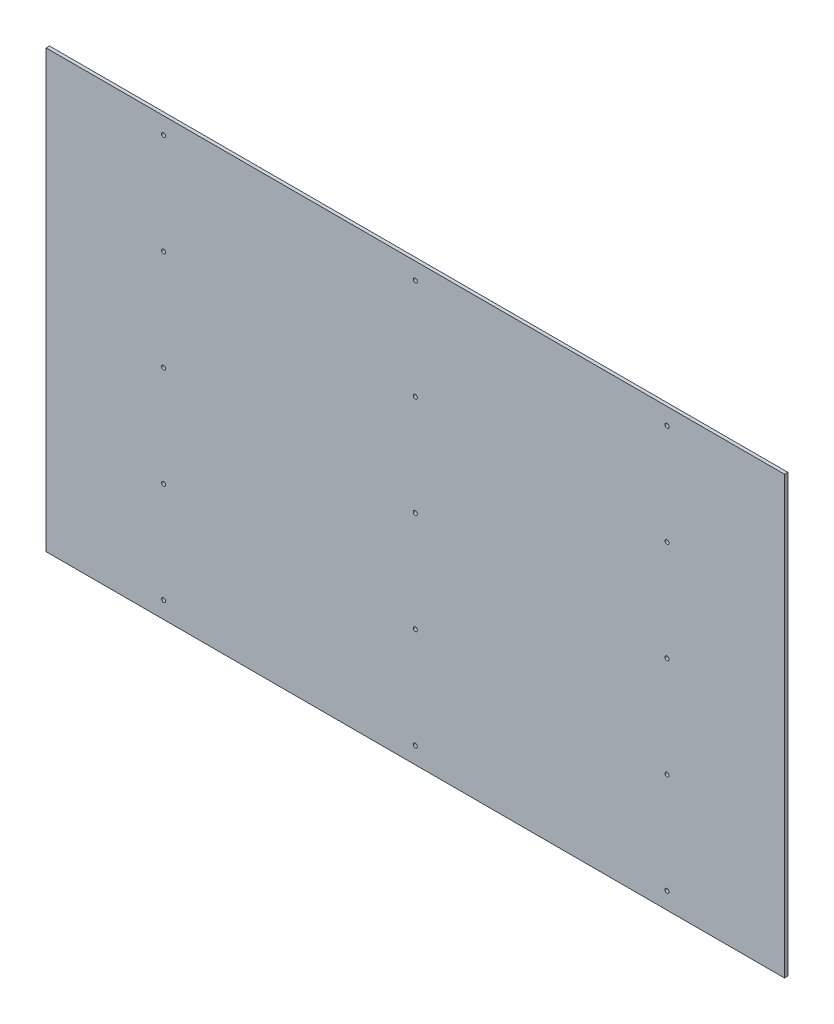
SolidWorks part; units mm, degrees
ref_plane "Płaszczyzna przednia" through (0, 0, 0) normal (0, 0, 1) x (1, 0, 0)
ref_plane "Płaszczyzna górna" through (0, 0, 0) normal (0, 1, 0) x (1, 0, 0)
ref_plane "Płaszczyzna prawa" through (0, 0, 0) normal (1, 0, 0) x (0, 0, -1)
sketch "Szkic1" plane through (0, 0, 0) normal (0, 0, 1) x (1, 0, 0)
  line L1 (-1100, -650) -> (1100, -650)
  line L2 (-1100, -650) -> (-1100, 650)
  line L3 (-1100, 650) -> (1100, 650)
  line L4 (1100, -650) -> (1100, 650)
  line L5 (-1100, -650) -> (1100, 650) construction
  line L6 (-1100, 650) -> (1100, -650) construction
  point P0 (0, 0)
  dimension "D1" = 2200
  dimension "D2" = 1300
extrude "Dodanie-wyciągnięcie1" add sketch "Szkic1" along normal blind 10
hole_wizard "Otwór pod śrubę M101" positions "Szkic2" profile "Szkic3" hole size "M10" standard "Ansi Metric" end condition through all
sketch "Szkic2" plane through (0, 0, 10) normal (0, 0, 1) x (1, 0, 0)
  line L0 (-1100, 650) -> (-1100, -650) construction
  line L2 (-1100, -650) -> (1100, -650) construction
  point P0 (-750, -600)
  dimension "D1" = 350
  dimension "D2" = 50
sketch "Szkic3" plane through (-750, -600, 10) normal (1, 0, 0) x (0, -1, 0)
  line L0 (0, 0) -> (0, 10)
  line L1 (0, 10) -> (6, 10)
  line L2 (6, 10) -> (6, 0)
  line L5 (6, 0) -> (0, 0)
  line L11 (0, -6.35) -> (0, 107.95) construction
  dimension "Średnica otworu na wylot" = 12
  dimension "Głębokość otworu na wylot" = 10
pattern_linear "Szyk liniowy1" count 5 spacing 300 along (0, 1, 0) count 3 spacing 750 along (1, 0, 0) of "Otwór pod śrubę M101"
